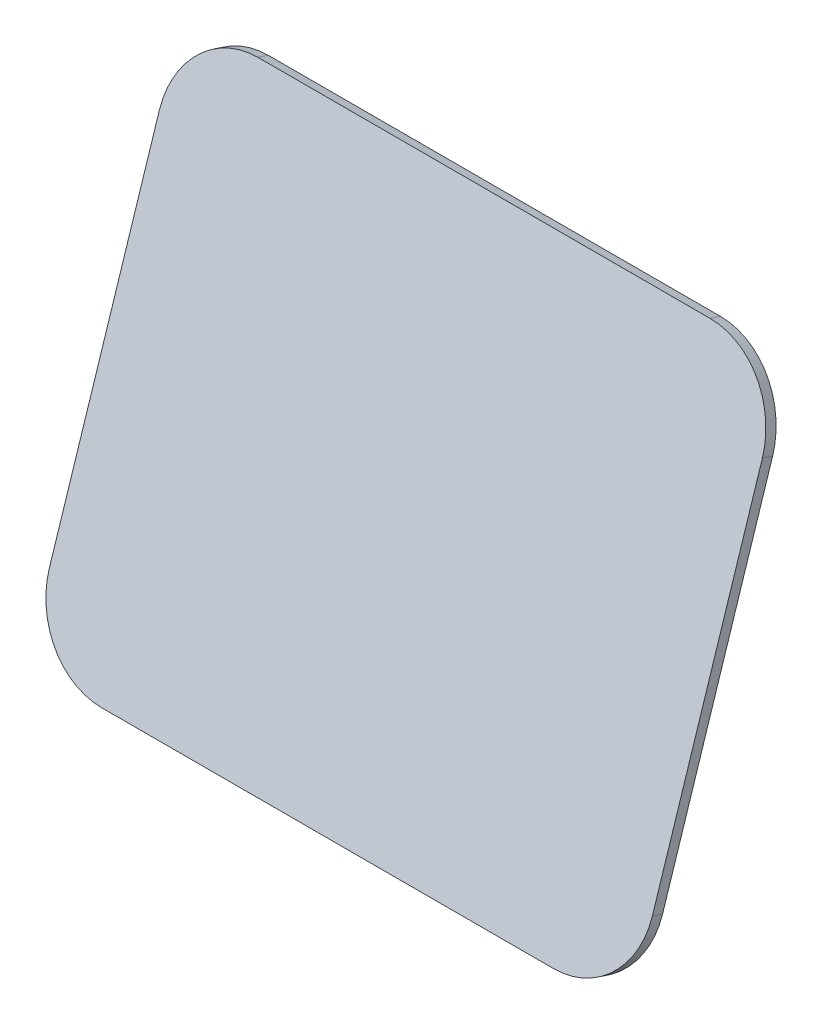
SolidWorks part; units mm, degrees
ref_plane "Front Plane" through (0, 0, 0) normal (0, 0, 1) x (1, 0, 0)
ref_plane "Top Plane" through (0, 0, 0) normal (0, 1, 0) x (1, 0, 0)
ref_plane "Right Plane" through (0, 0, 0) normal (1, 0, 0) x (0, 0, -1)
sketch "Sketch1" plane through (0, 68.2539, 211.8868) normal (0, 0.3066, 0.9518) x (1, 0, 0)
  line L0 (84, 109.8726) -> (84, 9.8726)
  line L1 (63, -11.1274) -> (-63, -11.1274)
  line L2 (-84, 9.8726) -> (-84, 109.8726)
  line L3 (-63, 130.8726) -> (63, 130.8726)
  line L4 (84, 76.8726) -> (84, 91.8726) construction
  line L6 (60, 121.8726) -> (-60, 121.8726) construction
  line L7 (-75, 106.8726) -> (-75, 12.8726) construction
  line L8 (-60, -2.1274) -> (60, -2.1274) construction
  arc A0 (84, 9.8726) -> (63, -11.1274) centre (63, 9.8726) cw
  arc A1 (-63, -11.1274) -> (-84, 9.8726) centre (-63, 9.8726) cw
  arc A2 (-84, 109.8726) -> (-63, 130.8726) centre (-63, 109.8726) cw
  arc A3 (84, 109.8726) -> (63, 130.8726) centre (63, 109.8726) ccw
  dimension "D4" = 21
  dimension "D1" = 9
  dimension "D2" = 9
  dimension "D3" = 9
extrude "Boss-Extrude1" add sketch "Sketch1" along normal blind 3
